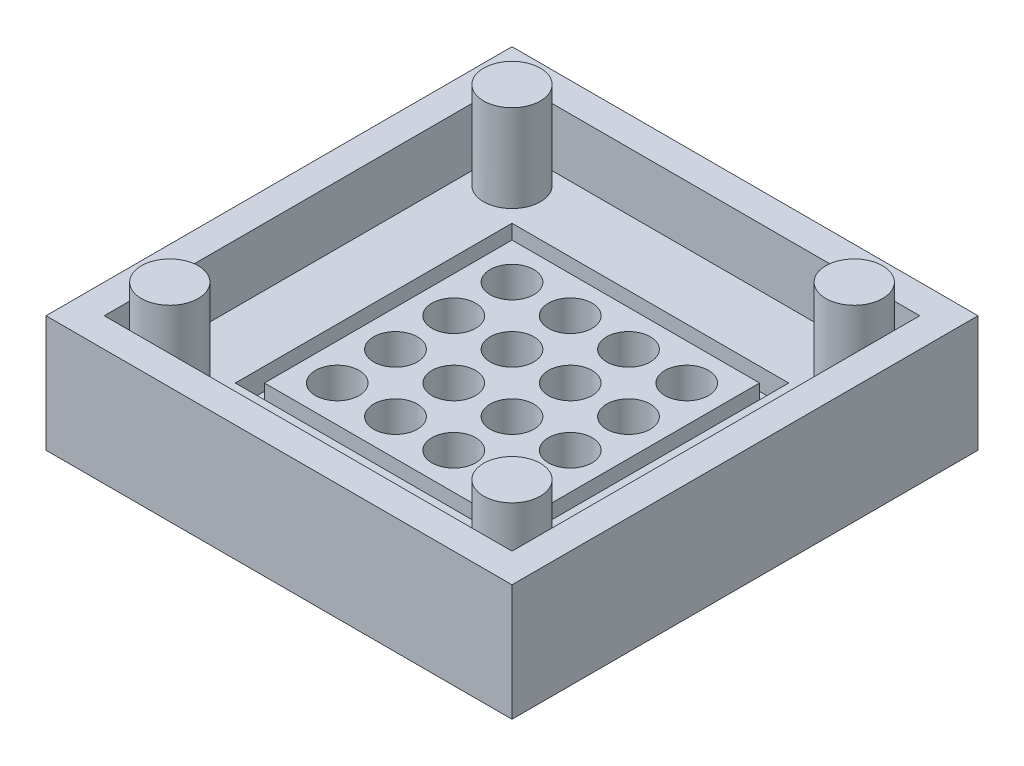
SolidWorks part; units mm, degrees
ref_plane "Front Plane" through (0, 0, 0) normal (0, 0, 1) x (1, 0, 0)
ref_plane "Top Plane" through (0, 0, 0) normal (0, 1, 0) x (1, 0, 0)
ref_plane "Right Plane" through (0, 0, 0) normal (1, 0, 0) x (0, 0, -1)
sketch "Sketch1" plane through (0, 0, 0) normal (0, 1, 0) x (1, 0, 0)
  line L1 (-16, -16) -> (16, -16)
  line L2 (-16, -16) -> (-16, 16)
  line L3 (-16, 16) -> (16, 16)
  line L4 (16, -16) -> (16, 16)
  line L5 (-16, -16) -> (16, 16) construction
  line L6 (-16, 16) -> (16, -16) construction
  point P0 (0, 0)
  dimension "D1" = 32
extrude "Boss-Extrude1" add sketch "Sketch1" along normal blind 8
sketch "Sketch2" plane through (0, 8, 0) normal (0, 1, 0) x (1, 0, 0)
  line L0 (-16, -16) -> (16, -16) construction
  line L1 (-14, -14) -> (14, -14)
  line L2 (-14, -14) -> (-14, 14)
  line L3 (-14, 14) -> (14, 14)
  line L4 (14, -14) -> (14, 14)
  line L5 (-14, -14) -> (14, 14) construction
  line L6 (-14, 14) -> (14, -14) construction
  point P0 (0, 0)
  dimension "D1" = 2
extrude "Cut-Extrude1" cut sketch "Sketch2" against normal blind 4
sketch "Sketch3" plane through (0, 4, 0) normal (0, 1, 0) x (1, 0, 0)
  line L1 (-9.5, -9.5) -> (9.5, -9.5)
  line L2 (-9.5, -9.5) -> (-9.5, 9.5)
  line L3 (-9.5, 9.5) -> (9.5, 9.5)
  line L4 (9.5, -9.5) -> (9.5, 9.5)
  line L5 (-9.5, -9.5) -> (9.5, 9.5) construction
  line L6 (-9.5, 9.5) -> (9.5, -9.5) construction
  point P0 (0, 0)
  dimension "D1" = 19
extrude "Cut-Extrude2" cut sketch "Sketch3" against normal blind 1.5
sketch "Sketch4" plane through (0, 2.5, 0) normal (0, 1, 0) x (1, 0, 0)
  line L0 (-9.5, -9.5) -> (9.5, -9.5) construction
  line L1 (-8.5, -8.5) -> (8.5, -8.5)
  line L2 (-8.5, -8.5) -> (-8.5, 8.5)
  line L3 (-8.5, 8.5) -> (8.5, 8.5)
  line L4 (8.5, -8.5) -> (8.5, 8.5)
  line L5 (-8.5, -8.5) -> (8.5, 8.5) construction
  line L6 (-8.5, 8.5) -> (8.5, -8.5) construction
  point P0 (0, 0)
  dimension "D1" = 1
extrude "Boss-Extrude2" add sketch "Sketch4" along normal blind 1.5
sketch "Sketch6" plane through (0, 4, 0) normal (0, 1, 0) x (1, 0, 0)
  line L0 (-9.5, 9.5) -> (-14, 14) construction
  line L1 (0, 14) -> (0, -14) construction
  line L2 (14, 14) -> (-14, 14) construction
  line L3 (-14, -14) -> (14, -14) construction
  line L4 (-14, 0) -> (14, 0) construction
  line L5 (-14, 14) -> (-14, -14) construction
  line L6 (14, -14) -> (14, 14) construction
  circle A0 centre (-11.75, 11.75) radius 1.95
  circle A1 centre (11.75, 11.75) radius 1.95
  circle A2 centre (11.75, -11.75) radius 1.95
  circle A3 centre (-11.75, -11.75) radius 1.95
  dimension "D1" = 3.9
extrude "Boss-Extrude3" add sketch "Sketch6" along normal blind 6
sketch "Sketch7" plane through (0, 4, 0) normal (0, 1, 0) x (1, 0, 0)
  line L0 (-6, 6) -> (6, -6) construction
  line L1 (6, -6) -> (6, 6) construction
  line L2 (6, 6) -> (-6, -6) construction
  circle A0 centre (-6, -6) radius 1.5
  circle A1 centre (-2, -6) radius 1.5
  circle A2 centre (2, -6) radius 1.5
  circle A3 centre (6, -6) radius 1.5
  circle A4 centre (-2, -2) radius 1.5
  circle A5 centre (2, -2) radius 1.5
  circle A6 centre (6, -2) radius 1.5
  circle A7 centre (-2, 2) radius 1.5
  circle A8 centre (2, 2) radius 1.5
  circle A9 centre (6, 2) radius 1.5
  circle A10 centre (-2, 6) radius 1.5
  circle A11 centre (2, 6) radius 1.5
  circle A12 centre (6, 6) radius 1.5
  circle A13 centre (-6, -2) radius 1.5
  circle A14 centre (-6, 2) radius 1.5
  circle A15 centre (-6, 6) radius 1.5
  point P2 (0, 0)
  dimension "D3" = 3
  dimension "D4" = 4
  dimension "D1" = 4
  dimension "D2" = 4
extrude "Cut-Extrude3" cut sketch "Sketch7" against normal blind 3
